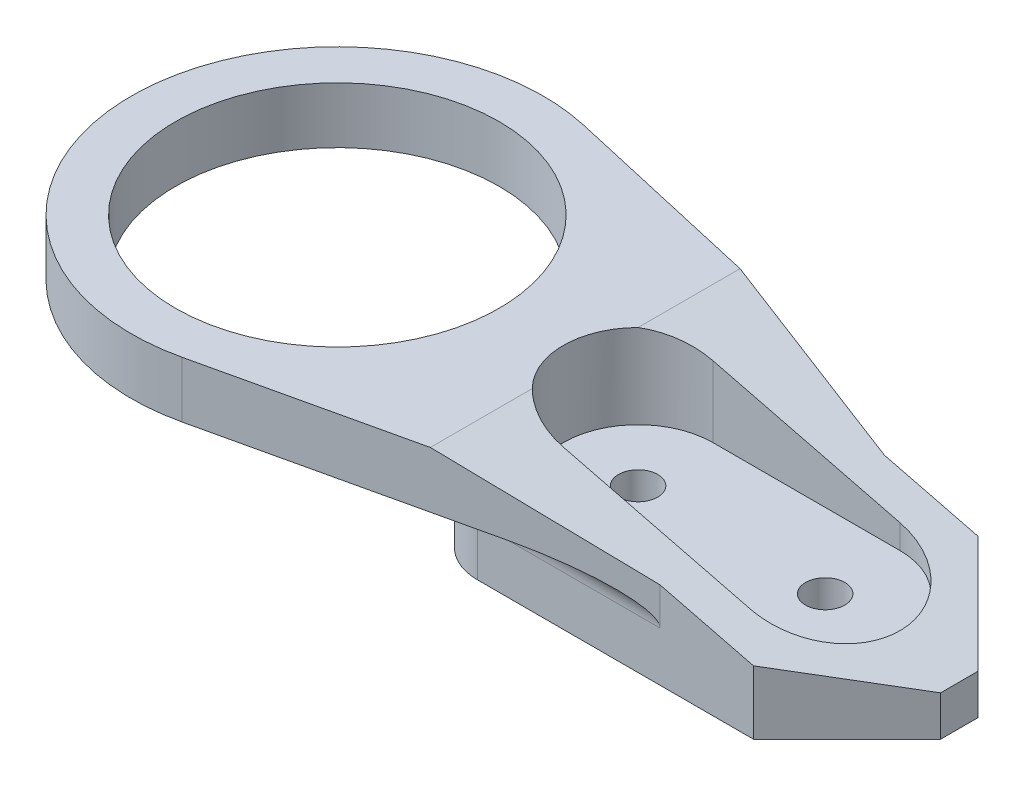
SolidWorks part; units mm, degrees
material "Tough 2000"
ref_plane "Front Plane" through (0, 0, 0) normal (0, 0, 1) x (1, 0, 0)
ref_plane "Top Plane" through (0, 0, 0) normal (0, 1, 0) x (1, 0, 0)
ref_plane "Right Plane" through (0, 0, 0) normal (1, 0, 0) x (0, 0, -1)
sketch "Sketch1" plane through (0, 0, 0) normal (0, 0, 1) x (1, 0, 0)
  line L0 (0, 0) -> (0, 7.15)
  line L1 (0, 7.15) -> (25, 7.15)
  line L2 (25, 7.15) -> (25, 0)
  line L3 (25, 0) -> (0, 0)
extrude "Boss-Extrude1" add sketch "Sketch1" along normal blind 12
sketch "Sketch2" plane through (0, 7.15, 0) normal (0, 1, 0) x (1, 0, 0)
  line L0 (0, -6) -> (-8.25, -6) construction
  line L1 (0, -12) -> (0, 0) construction
  line L3 (25, 0) -> (0, 0) construction
  line L5 (25, -12) -> (0, -12) construction
  line L8 (15, -6) -> (15, 0)
  line L11 (15, 0) -> (-5.8049, 4.7375)
  line L12 (15, -6) -> (15, -12)
  line L13 (15, -12) -> (-5.8049, -16.7375)
  arc A6 (-5.8049, 4.7375) -> (-5.8049, -16.7375) centre (-8.25, -6) ccw
extrude "Boss-Extrude2" add sketch "Sketch2" against normal blind 3
sketch "Sketch3" plane through (0, 4.15, 0) normal (0, -1, 0) x (1, 0, 0)
  line L0 (-8.25, 6) -> (2.25, 6) construction
  line L1 (2.25, 6) -> (2.25, 12)
  line L2 (0, 12) -> (25, 12) construction
  line L3 (2.25, 12) -> (0, 12)
  line L4 (0, 12) -> (0, 0)
  line L5 (0, 0) -> (2.25, 0)
  line L6 (15, 0) -> (0, 0) construction
  line L7 (2.25, 0) -> (2.25, 6)
  circle A0 centre (-8.25, 6) radius 11.0124 construction
extrude "Cut-Extrude1" cut sketch "Sketch3" along normal blind 21
sketch "Sketch4" plane through (0, 4.15, 0) normal (0, -1, 0) x (1, 0, 0)
  circle A2 centre (-8.25, 6) radius 8.65
extrude "Cut-Extrude2" cut sketch "Sketch4" against normal blind 10
chamfer "Chamfer1" distance 5 distance2 20 1 edges at (25, 7.15, 6)
chamfer "Chamfer2" distance 5 angle 45 2 edges at (25, 1.075, 12) (25, 1.075, 0)
sketch "Sketch6" plane through (0, 7.15, 0) normal (0, 1, 0) x (1, 0, 0)
  line L0 (-0.0037, -6) -> (7.8299, -6) construction
  line L1 (7.8299, -6) -> (17.8299, -6) construction
  circle A0 centre (-8.5537, -6) radius 8.55 construction
  circle A1 centre (7.8299, -6) radius 1.05
  circle A2 centre (17.8299, -6) radius 1.05
  dimension "D1" = 10
extrude "Cut-Extrude3" cut sketch "Sketch6" against normal blind 10
sketch "Sketch7" plane through (0, 7.15, 0) normal (0, 1, 0) x (1, 0, 0)
  line L0 (7.8299, -2) -> (17.8299, -2)
  line L1 (17.8299, -10) -> (7.8299, -10)
  arc A0 (7.8299, -2) -> (7.8299, -10) centre (7.8299, -6) ccw
  arc A1 (17.8299, -10) -> (17.8299, -2) centre (17.8299, -6) ccw
extrude "Cut-Extrude4" cut sketch "Sketch7" against normal blind 4.5
fillet "Fillet1" radius 3 2 edges at (2.25, 2.075, 12) (2.25, 2.075, 0)
fillet "Fillet2" radius 1.5 5 edges at (10.125, 4.15, 12) (3.1287, 4.15, 11.1213) (2.25, 4.15, 6) (3.1287, 4.15, 0.8787) (10.125, 4.15, 0)
